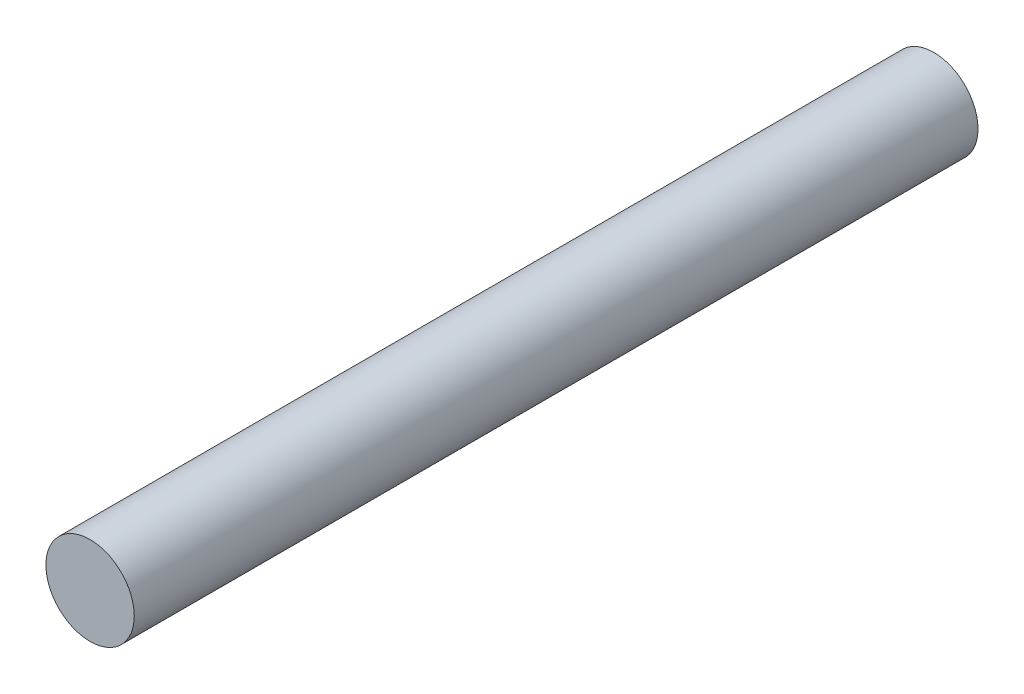
SolidWorks part; units mm, degrees
ref_plane "Front Plane" through (0, 0, 0) normal (0, 0, 1) x (1, 0, 0)
ref_plane "Top Plane" through (0, 0, 0) normal (0, 1, 0) x (1, 0, 0)
ref_plane "Right Plane" through (0, 0, 0) normal (1, 0, 0) x (0, 0, -1)
sketch "Sketch9" plane through (0, 0, 0) normal (0, 0, 1) x (1, 0, 0)
  circle A0 centre (0, 0) radius 1.27
extrude "Extrude2" add sketch "Sketch9" along normal blind 24.257
sketch "Sketch10" plane through (0, 0, 24.257) normal (0, 0, 1) x (1, 0, 0)
  line L0 (0, 0) -> (0, 1.27) construction
  circle A0 centre (0, 0) radius 1.27 construction
